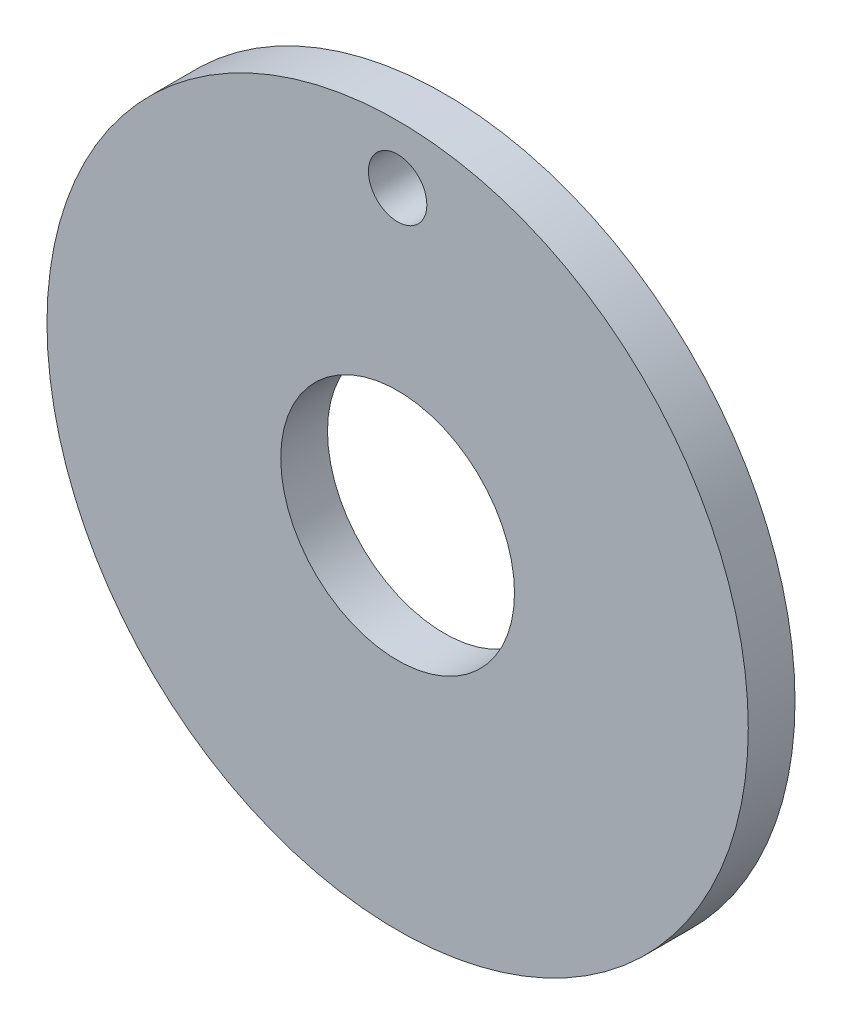
SolidWorks part; units mm, degrees
material "PVC Rigid"
ref_plane "Front Plane" through (0, 0, 0) normal (0, 0, 1) x (1, 0, 0)
ref_plane "Top Plane" through (0, 0, 0) normal (0, 1, 0) x (1, 0, 0)
ref_plane "Right Plane" through (0, 0, 0) normal (1, 0, 0) x (0, 0, -1)
sketch "Sketch1" plane through (0, 0, 0) normal (0, 0, 1) x (1, 0, 0)
  circle A0 centre (0, 0) radius 19.05
  circle A1 centre (0, 0) radius 6.35
  dimension "D1" = 38.1
  dimension "D2" = 12.7
extrude "Boss-Extrude1" add sketch "Sketch1" along normal blind 2.54
sketch "Sketch2" plane through (0, 0, 2.54) normal (0, 0, 1) x (1, 0, 0)
  line L0 (0, 0) -> (0, 14.2875) construction
  circle A0 centre (0, 15.875) radius 1.5875
  dimension "D2" = 3.175
  dimension "D1" = 14.2875
extrude "Cut-Extrude1" cut sketch "Sketch2" against normal through all contours A0
